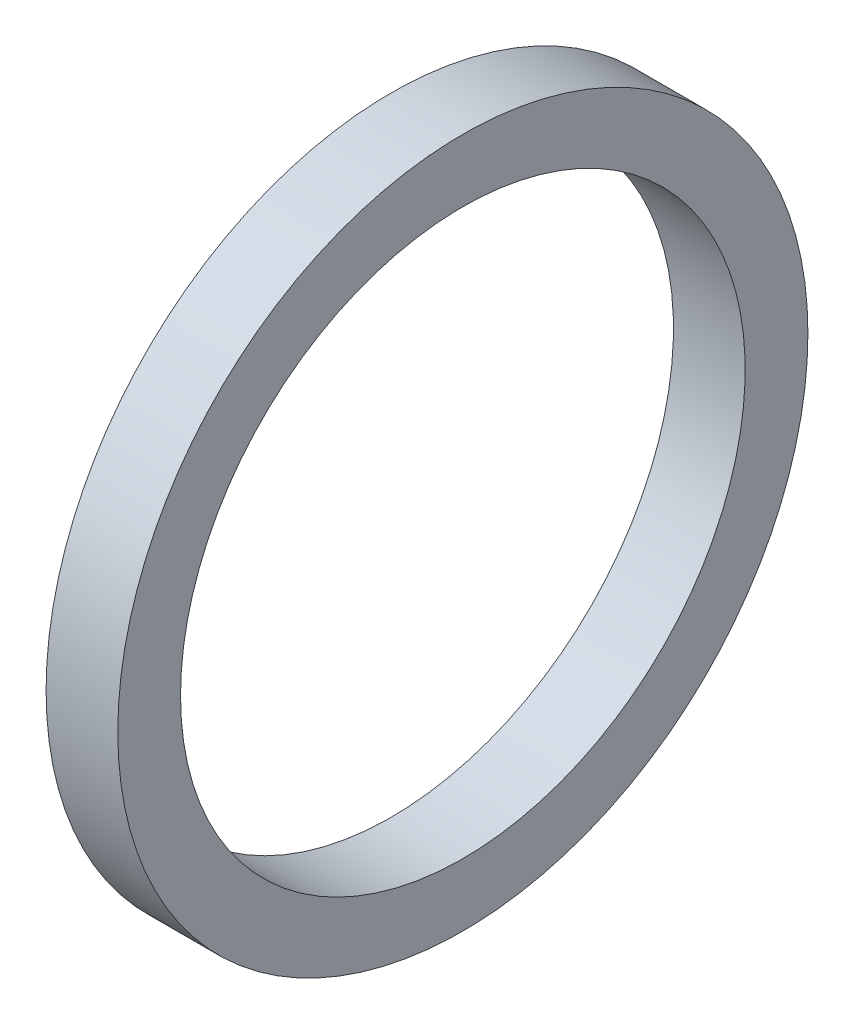
SolidWorks part; units mm, degrees
ref_plane "Front Plane" through (0, 0, 0) normal (0, 0, 1) x (1, 0, 0)
ref_plane "Top Plane" through (0, 0, 0) normal (0, 1, 0) x (1, 0, 0)
ref_plane "Right Plane" through (0, 0, 0) normal (1, 0, 0) x (0, 0, -1)
sketch "Sketch1" plane through (0, 0, 0) normal (0, 0, 1) x (1, 0, 0)
  line L0 (-43.7166, 0) -> (79.6876, 0) construction
  line L2 (0, -8.001) -> (2.032, -8.001)
  line L3 (0, -8.001) -> (0, -9.779)
  line L4 (0, -9.779) -> (2.032, -9.779)
  line L5 (2.032, -8.001) -> (2.032, -9.779)
  dimension "A" = 16.002
  dimension "B" = 19.558
  dimension "C" = 2.032
revolve "Revolve1" add sketch "Sketch1" angle 360 about L0
sketch "Sketch2" [suppressed] plane through (0, 0, 0) normal (0, 0, 1) x (1, 0, 0)
  line L0 (-34.685, 0) -> (47.6686, 0) construction
  circle A0 centre (2.54, -5.715) radius 0.762
  dimension "D1" = 2.54
  dimension "E" = 1.524
  dimension "D" = 11.938
revolve "Revolve3" [suppressed] add sketch "Sketch2" angle 360 about L0
